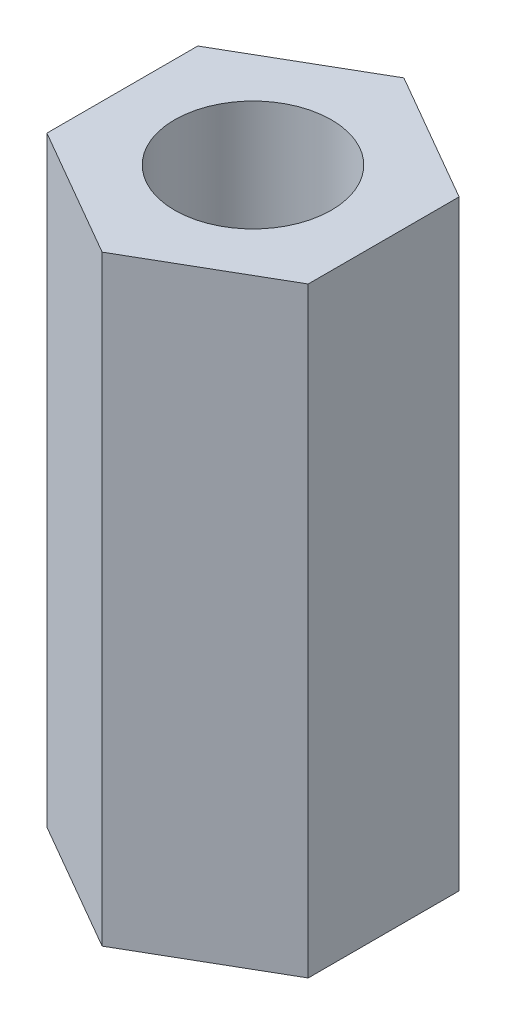
SolidWorks part; units mm, degrees
ref_plane "Спереди" through (0, 0, 0) normal (0, 0, 1) x (1, 0, 0)
ref_plane "Сверху" through (0, 0, 0) normal (0, 1, 0) x (1, 0, 0)
ref_plane "Справа" through (0, 0, 0) normal (1, 0, 0) x (0, 0, -1)
sketch "Эскиз1" plane through (0, 0, 0) normal (0, 1, 0) x (1, 0, 0)
  line L0 (0, 0) -> (0, 2.8868) construction
  line L1 (0, -2.8868) -> (2.5, -1.4434)
  line L2 (2.5, -1.4434) -> (2.5, 1.4434)
  line L3 (2.5, 1.4434) -> (0, 2.8868)
  line L4 (0, 2.8868) -> (-2.5, 1.4434)
  line L5 (-2.5, 1.4434) -> (-2.5, -1.4434)
  line L6 (-2.5, -1.4434) -> (0, -2.8868)
  circle A0 centre (0, 0) radius 2.5 construction
  circle A1 centre (0, 0) radius 1.5
  dimension "D2" = 3
  dimension "D1" = 5
extrude "Бобышка-Вытянуть1" add sketch "Эскиз1" along normal blind 11.5
